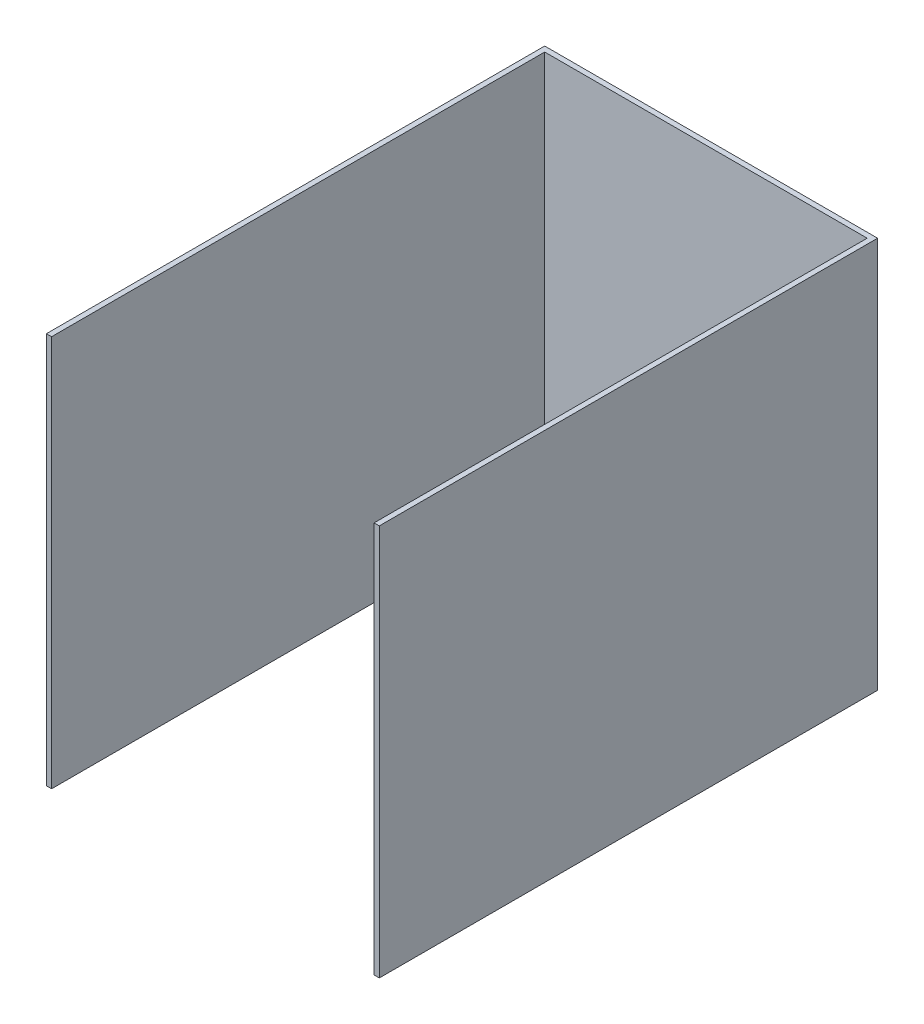
SolidWorks part; units mm, degrees
ref_plane "Front Plane" through (0, 0, 0) normal (0, 0, 1) x (1, 0, 0)
ref_plane "Top Plane" through (0, 0, 0) normal (0, 1, 0) x (1, 0, 0)
ref_plane "Right Plane" through (0, 0, 0) normal (1, 0, 0) x (0, 0, -1)
sketch "Sketch1" plane through (0, 0, 0) normal (0, 0, 1) x (1, 0, 0)
  line L1 (0, 0) -> (-203.2, 0)
  line L2 (0, 0) -> (0, 239)
  line L3 (0, 239) -> (-203.2, 239)
  line L6 (-203.2, 239) -> (-203.2, 0)
  dimension "D1" = 203.2
  dimension "D2" = 239
extrude "Boss-Extrude2" add sketch "Sketch1" along normal blind 3.175
sketch "Sketch2" plane through (0, 0, 3.175) normal (0, 0, 1) x (1, 0, 0)
  line L0 (-101.6, 239) -> (-101.6, 0) construction
  line L1 (-203.2, 239) -> (-200.025, 239)
  line L2 (-203.2, 239) -> (-203.2, 0)
  line L3 (-203.2, 0) -> (-200.025, 0)
  line L4 (-200.025, 239) -> (-200.025, 0)
  line L5 (0, 239) -> (-203.2, 239) construction
  line L6 (-203.2, 0) -> (0, 0) construction
  line L7 (-3.175, 239) -> (-3.175, 0)
  line L8 (0, 239) -> (0, 0)
  line L9 (-3.175, 0) -> (0, 0)
  line L10 (-3.175, 239) -> (0, 239)
  dimension "D1" = 3.175
  dimension "D2" = 239
extrude "Boss-Extrude5" add sketch "Sketch2" along normal blind 301
